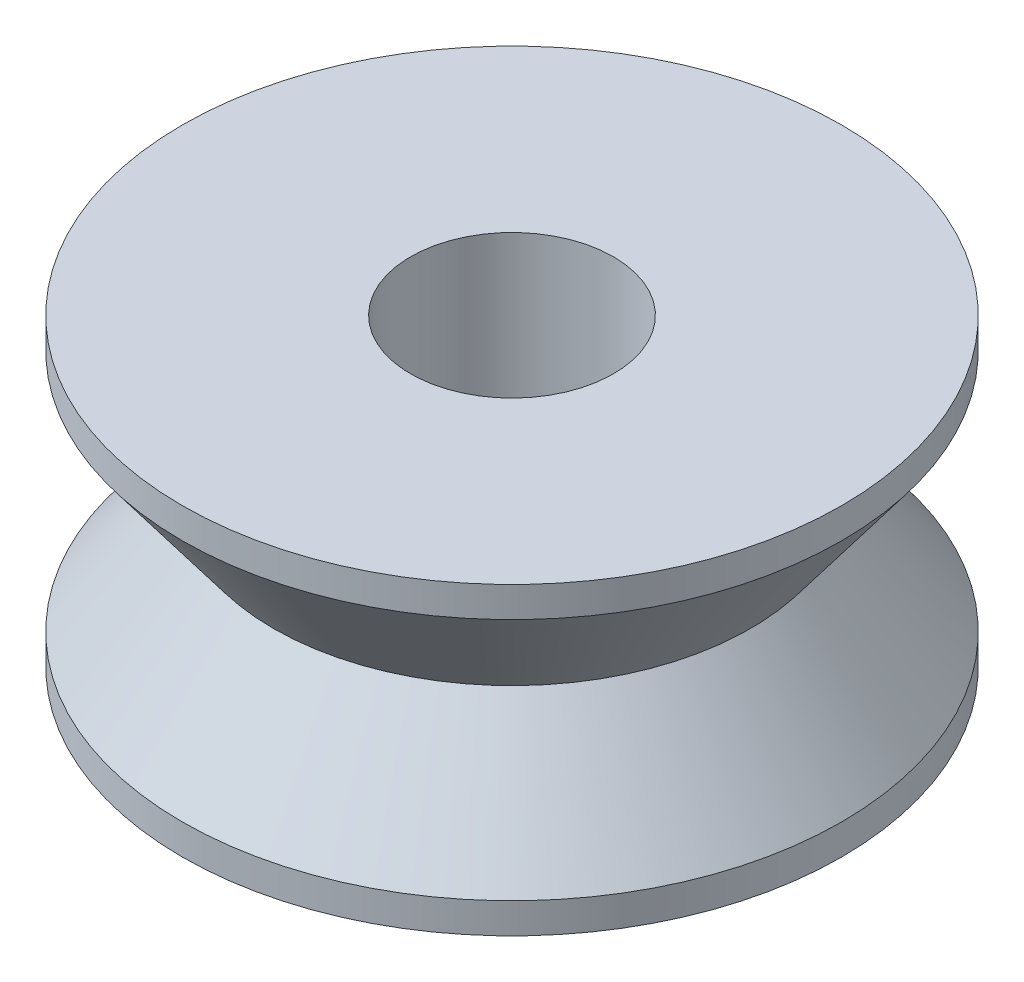
SolidWorks part; units mm, degrees
ref_plane "Front Plane" through (0, 0, 0) normal (0, 0, 1) x (1, 0, 0)
ref_plane "Top Plane" through (0, 0, 0) normal (0, 1, 0) x (1, 0, 0)
ref_plane "Right Plane" through (0, 0, 0) normal (1, 0, 0) x (0, 0, -1)
sketch "Sketch1" plane through (0, 0, 0) normal (0, 0, 1) x (1, 0, 0)
  line L0 (-6.5, 3) -> (-6.5, 2.4)
  line L1 (-6.5, 2.4) -> (-4.7, 0)
  line L2 (-4.7, 0) -> (-6.5, -2.4)
  line L3 (-6.5, -2.4) -> (-6.5, -3)
  line L4 (-6.5, -3) -> (-2, -3)
  line L5 (-2, -3) -> (-2, 3)
  line L6 (-2, 3) -> (-6.5, 3)
  line L7 (0, 0) -> (0, 1.6375) construction
  point P10 (-4.7, 1.5556)
  dimension "D1" = 13
  dimension "D2" = 4
  dimension "D3" = 6
  dimension "D4" = 4.8
  dimension "D5" = 1.8
revolve "Revolve1" add sketch "Sketch1" angle 360 about L7
